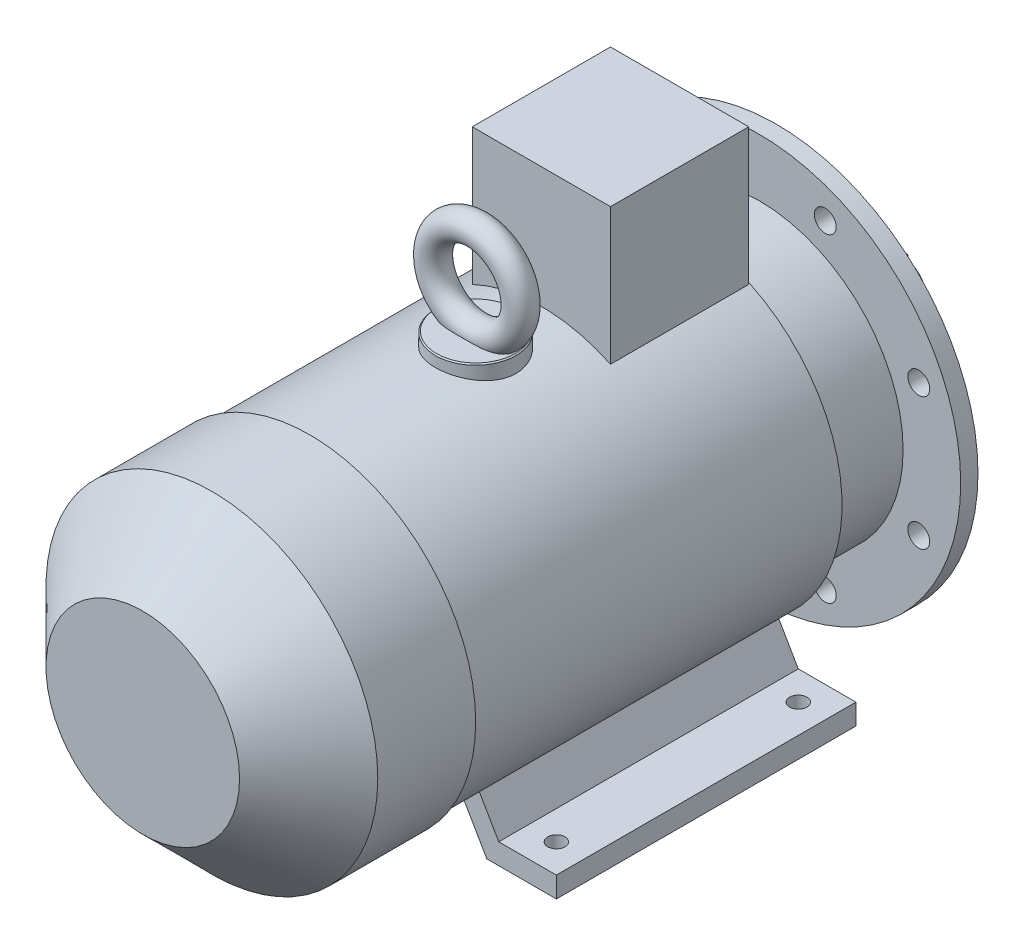
SolidWorks part; units mm, degrees
material "Ст.3 ГОСТ 380-88"
ref_plane "Спереди" through (0, 0, 0) normal (0, 0, 1) x (1, 0, 0)
ref_plane "Сверху" through (0, 0, 0) normal (0, 1, 0) x (1, 0, 0)
ref_plane "Справа" through (0, 0, 0) normal (1, 0, 0) x (0, 0, -1)
sketch "Эскиз1" plane through (0, 0, 0) normal (0, 0, 1) x (1, 0, 0)
  circle A0 centre (0, 0) radius 21
  dimension "D1" = 42
extrude "Вытянуть1" add sketch "Эскиз1" along normal blind 110
sketch "Эскиз2" plane through (0, 0, 0) normal (0, 0, -1) x (-1, 0, 0)
  line L0 (0, 0) -> (0, 24.6027) construction
  line L2 (-4, 24) -> (4, 24)
  line L3 (-4, 24) -> (-4, 16)
  line L4 (-4, 16) -> (4, 16)
  line L5 (4, 24) -> (4, 16)
  circle A1 centre (0, 0) radius 21 construction
  dimension "D1" = 8
  dimension "D2" = 8
  dimension "D3" = 45
extrude "Вытянуть2" add sketch "Эскиз2" against normal blind 55 and the other way blind 0.1
sketch "Эскиз3" plane through (0, 0, 110) normal (0, 0, 1) x (1, 0, 0)
  circle A0 centre (0, 0) radius 175
  dimension "D1" = 350
extrude "Вытянуть3" add sketch "Эскиз3" along normal blind 15
sketch "Эскиз4" plane through (0, 0, 110) normal (0, 0, -1) x (-1, 0, 0)
  circle A0 centre (0, 0) radius 125
  circle A1 centre (0, 0) radius 116
  dimension "D1" = 250
  dimension "D2" = 232
extrude "Вытянуть4" add sketch "Эскиз4" along normal blind 5
sketch "Эскиз5" plane through (0, 0, 110) normal (0, 0, -1) x (-1, 0, 0)
  circle A0 centre (0, 0) radius 116
  circle A1 centre (0, 0) radius 40
  dimension "D1" = 232
  dimension "D2" = 80
extrude "Вырез-Вытянуть1" cut sketch "Эскиз5" against normal blind 8
chamfer "Фаска1" distance 1 angle 45 3 edges at (-125, 0, 105) (-40, 0, 110) (0, -21, 0)
sketch "Эскиз6" plane through (0, 0, 110) normal (0, 0, -1) x (-1, 0, 0)
  line L0 (0, 0) -> (0, 218.5331) construction
  line L1 (0, 0) -> (-85.0868, 205.4176) construction
  circle A0 centre (-57.4025, 138.5819) radius 9.5
  circle A2 centre (57.4025, 138.5819) radius 9.5
  circle A3 centre (138.5819, 57.4025) radius 9.5
  circle A4 centre (138.5819, -57.4025) radius 9.5
  circle A5 centre (57.4025, -138.5819) radius 9.5
  circle A6 centre (-57.4025, -138.5819) radius 9.5
  circle A7 centre (-138.5819, -57.4025) radius 9.5
  circle A8 centre (-138.5819, 57.4025) radius 9.5
  dimension "D2" = 19
  dimension "D1" = 22.5
  dimension "D3" = 150
  dimension "D4" = 150
  dimension "D5" = 150
extrude "Вырез-Вытянуть2" cut sketch "Эскиз6" against normal through all
sketch "Эскиз7" plane through (0, 0, 125) normal (0, 0, 1) x (1, 0, 0)
  circle A0 centre (0, 0) radius 125
  dimension "D1" = 250
extrude "Вытянуть5" add sketch "Эскиз7" along normal blind 68
sketch "Эскиз8" plane through (0, 0, 193) normal (0, 0, 1) x (1, 0, 0)
  circle A0 centre (0, 0) radius 140
  dimension "D1" = 280
extrude "Вытянуть6" add sketch "Эскиз8" along normal blind 322
sketch "Эскиз9" plane through (0, 0, 515) normal (0, 0, 1) x (1, 0, 0)
  circle A0 centre (0, 0) radius 144
  dimension "D1" = 288
extrude "Вытянуть7" add sketch "Эскиз9" along normal blind 145
chamfer "Фаска2" distance 60 angle 45 1 edges at (144, 0, 660)
sketch "Эскиз10" plane through (0, 0, 193) normal (0, 0, -1) x (-1, 0, 0)
  line L0 (0, 0) -> (0, -216.5066) construction
  line L1 (-152, -160) -> (-91.6077, -160)
  line L2 (-91.6077, -160) -> (-51.9454, -91.303)
  line L3 (-51.9454, -91.303) -> (-67.5339, -82.303)
  line L4 (-67.5339, -82.303) -> (-102, -142)
  line L5 (-102, -142) -> (-152, -142)
  line L6 (-152, -142) -> (-152, -160)
  line L7 (91.6077, -160) -> (51.9454, -91.303)
  line L8 (152, -160) -> (91.6077, -160)
  line L9 (152, -142) -> (152, -160)
  line L10 (102, -142) -> (152, -142)
  line L11 (67.5339, -82.303) -> (102, -142)
  line L12 (51.9454, -91.303) -> (67.5339, -82.303)
  dimension "D1" = 18
  dimension "D2" = 18
  dimension "D3" = 30
  dimension "D4" = 50
  dimension "D5" = 152
  dimension "D6" = 160
  dimension "D7" = 105.0434
extrude "Вытянуть8" add sketch "Эскиз10" against normal blind 260
sketch "Эскиз11" plane through (0, -160, 0) normal (0, -1, 0) x (1, 0, 0)
  line L0 (-211.0007, 218) -> (224.3783, 218) construction
  line L1 (0, 0) -> (0, 657.2941) construction
  line L2 (-127, 218) -> (127, 218) construction
  line L3 (-127, 218) -> (-127, 428) construction
  circle A0 centre (-127, 218) radius 7.5
  circle A1 centre (127, 218) radius 7.5
  circle A2 centre (-127, 428) radius 7.5
  circle A3 centre (127, 428) radius 7.5
  dimension "D2" = 15
  dimension "D1" = 218
  dimension "D3" = 127
  dimension "D4" = 90
  dimension "D5" = 210
  dimension "D6" = 254
  dimension "D7" = 428
extrude "Вырез-Вытянуть3" cut sketch "Эскиз11" against normal up to next
sketch "Эскиз12" plane through (0, 0, 0) normal (0, 1, 0) x (1, 0, 0)
  line L0 (0, 0) -> (0, -277.4752) construction
  line L2 (-60, -194) -> (60, -194)
  line L3 (-60, -194) -> (-60, -314)
  line L4 (-60, -314) -> (60, -314)
  line L5 (60, -194) -> (60, -314)
  line L6 (140, -193) -> (-140, -193) construction
  dimension "D1" = 120
  dimension "D2" = 120
  dimension "D3" = 1
extrude "Вытянуть9" add sketch "Эскиз12" along normal blind 245
sketch "Эскиз13" plane through (0, 0, 0) normal (0, 1, 0) x (1, 0, 0)
  line L0 (0, -1) -> (0, -457.8467) construction
  line L1 (-21, -1) -> (21, -1) construction
  circle A0 centre (0, -371) radius 35
  dimension "D1" = 70
  dimension "D2" = 370
extrude "Вытянуть10" add sketch "Эскиз13" along normal blind 150
chamfer "Фаска3" distance 1 angle 45 1 edges at (0, 150, 406)
ref_plane "Плоскость1" through (0, 0, 370) normal (0, 0, 1) x (1, 0, 0)
sketch "Эскиз14" plane through (0, 0, 370) normal (0, 0, 1) x (1, 0, 0)
  line L0 (0, 0) -> (0, 273.5288) construction
  line L1 (34, 150) -> (-34, 150) construction
  circle A0 centre (0, 188) radius 38
  dimension "D1" = 76
sketch "Эскиз15" plane through (0, 0, 0) normal (1, 0, 0) x (0, 0, -1)
  line L0 (-370, 0) -> (-370, 273.5288) construction
  line L1 (-370, 226) -> (-370, 150) construction
  line L2 (-337, 150) -> (-405, 150) construction
  circle A0 centre (-370, 226) radius 12
  dimension "D1" = 24
  dimension "D2" = 76
sweep "По траектории1" add profiles "Эскиз15" path "Эскиз14"
sketch "Эскиз16" plane through (-60, 0, 0) normal (-1, 0, 0) x (0, 0, 1)
  line L0 (194, 245) -> (314, 245) construction
  line L1 (194, 245) -> (194, 126.4911) construction
  circle A0 centre (254, 185) radius 16
  dimension "D1" = 32
  dimension "D2" = 60
  dimension "D3" = 60
extrude "Вытянуть11" add sketch "Эскиз16" along normal blind 14
sketch "Эскиз17" plane through (-74, 0, 0) normal (-1, 0, 0) x (0, 0, 1)
  line L0 (254, 185) -> (254, 256.276) construction
  line L1 (254, 207.5167) -> (234.5, 196.2583)
  line L2 (234.5, 196.2583) -> (234.5, 173.7417)
  line L3 (234.5, 173.7417) -> (254, 162.4833)
  line L4 (254, 162.4833) -> (273.5, 173.7417)
  line L5 (273.5, 173.7417) -> (273.5, 196.2583)
  line L6 (273.5, 196.2583) -> (254, 207.5167)
  circle A0 centre (254, 185) radius 19.5 construction
  circle A1 centre (254, 185) radius 16 construction
  dimension "D1" = 39
extrude "Вытянуть12" add sketch "Эскиз17" along normal blind 16
sketch "Эскиз18" plane through (-90, 0, 0) normal (-1, 0, 0) x (0, 0, 1)
  circle A0 centre (254, 185) radius 7
  circle A1 centre (254, 185) radius 16 construction
  dimension "D1" = 14
extrude "Вырез-Вытянуть4" cut sketch "Эскиз18" against normal blind 16
